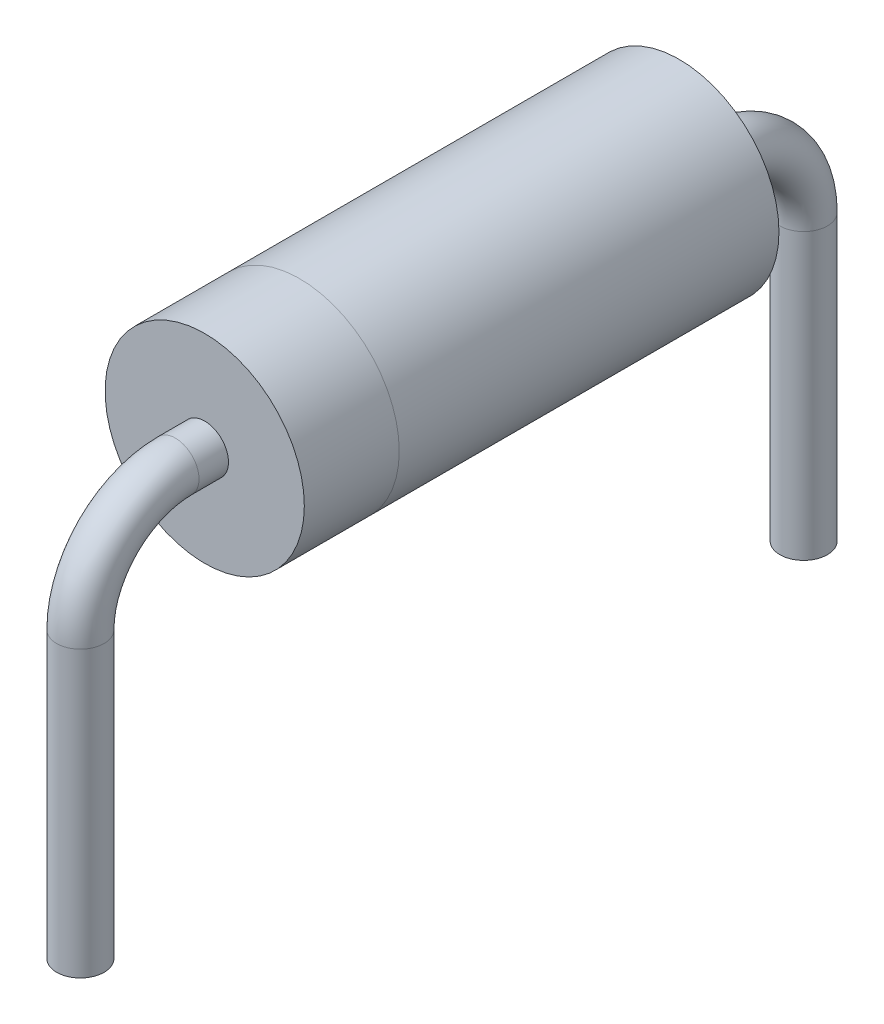
SolidWorks part; units mm, degrees
ref_plane "Plan de face" through (0, 0, 0) normal (0, 0, 1) x (1, 0, 0)
ref_plane "Plan de dessus" through (0, 0, 0) normal (0, 1, 0) x (1, 0, 0)
ref_plane "Plan de droite" through (0, 0, 0) normal (1, 0, 0) x (0, 0, -1)
sketch "Esquisse1" plane through (0, 0, 0) normal (0, 0, 1) x (1, 0, 0)
  circle A0 centre (0, 0) radius 1.05
  dimension "D1" = 2.1
extrude "Boss.-Extru.1" add sketch "Esquisse1" along normal blind 4
sketch "Esquisse2" plane through (0, 0, 4) normal (0, 0, 1) x (1, 0, 0)
  circle A0 centre (0, 0) radius 1.0495
  dimension "D1" = 2.099
extrude "Boss.-Extru.2" add sketch "Esquisse2" along normal blind 1
ref_plane "Plan1" through (0, 0, 5) normal (0, 0, 1) x (1, 0, 0)
sketch "Esquisse3" plane through (0, 0, 0) normal (1, 0, 0) x (0, 0, -1)
  line L0 (-5, 0) -> (-5.31, 0)
  line L1 (-5, 1.1544) -> (-5, -1.1544) construction
  line L2 (-6.31, -1) -> (-6.31, -4)
  arc A0 (-5.31, 0) -> (-6.31, -1) centre (-5.31, -1) ccw
  point P8 (-6.31, 0)
  dimension "D3" = 1
  dimension "D1" = 1.31
  dimension "D2" = 4
sketch "Esquisse4" plane through (0, 0, 5) normal (0, 0, 1) x (1, 0, 0)
  circle A0 centre (0, 0) radius 0.25
  dimension "D1" = 0.5
sweep "Balayage1" add profiles "Esquisse4" path "Esquisse3"
ref_plane "Plan2" through (0, 0, 2.5) normal (0, 0, 1) x (1, 0, 0)
mirror "Symétrie1" about plane through (0, 0, 2.5) normal (0, 0, 1) of "Balayage1"
sketch "Esquisse5" [suppressed] plane through (0, 0, 5) normal (0, 0, 1) x (1, 0, 0)
  circle A0 centre (0, 0) radius 0.25
extrude "Boss.-Extru.3" [suppressed] add sketch "Esquisse5" against normal up to surface (5 mm away) separate body
